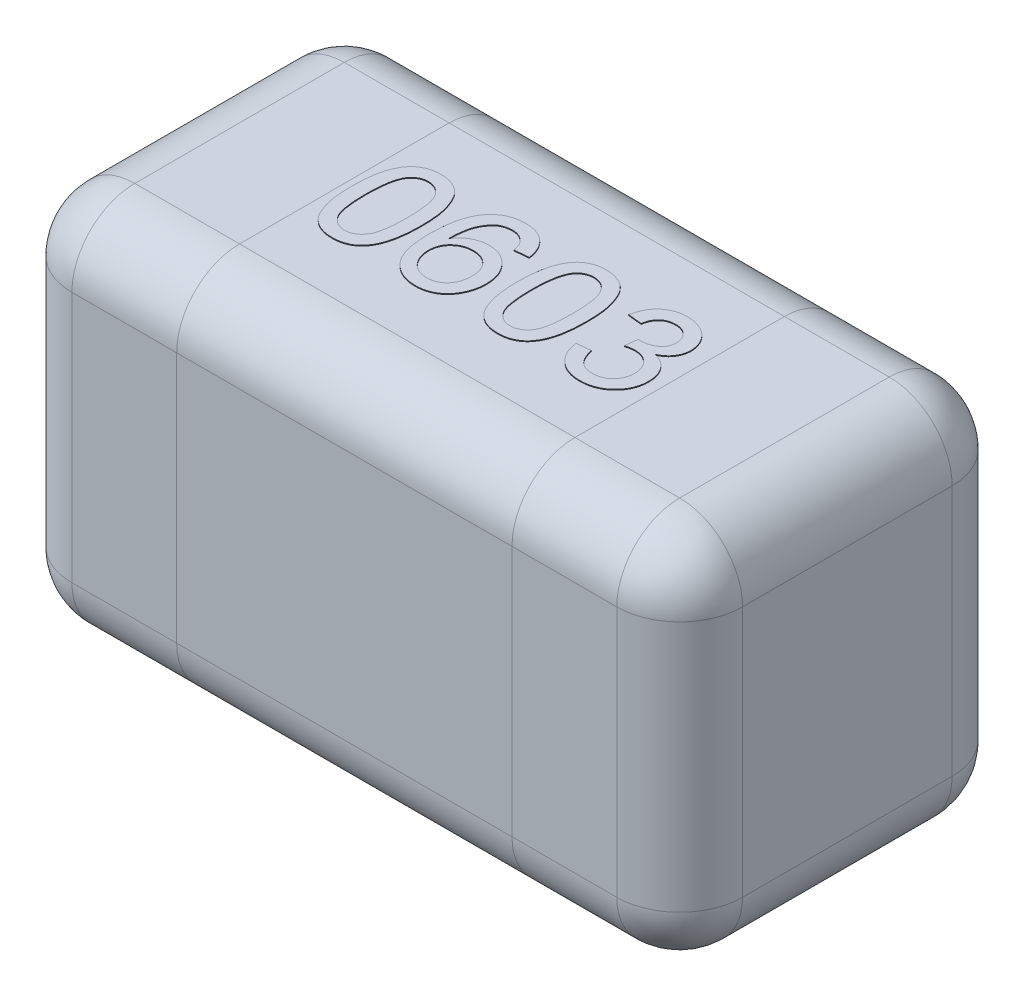
SolidWorks part; units mm, degrees
ref_plane "Front" through (0, 0, 0) normal (0, 0, 1) x (1, 0, 0)
ref_plane "Top" through (0, 0, 0) normal (0, 1, 0) x (1, 0, 0)
ref_plane "Right" through (0, 0, 0) normal (1, 0, 0) x (0, 0, -1)
sketch "Sketch1" plane through (0, 0, 0) normal (0, 1, 0) x (1, 0, 0)
  line L0 (0, -5.3126) -> (0, 5.729) construction
  line L1 (-6.1479, 0) -> (7.7291, 0) construction
  line L3 (-0.8, 0.4) -> (0.8, 0.4)
  line L4 (-0.8, 0.4) -> (-0.8, -0.4)
  line L5 (-0.8, -0.4) -> (0.8, -0.4)
  line L6 (0.8, 0.4) -> (0.8, -0.4)
  dimension "D1" = 1.6
  dimension "D2" = 0.8
extrude "Extrude1" add sketch "Sketch1" along normal blind 0.9
fillet "Fillet1" radius 0.15 12 edges at (0, 0.9, 0.4) (-0.8, 0.45, -0.4) (0, 0, -0.4) (-0.8, 0, 0) (-0.8, 0.45, 0.4) (0, 0, 0.4) (0.8, 0.45, 0.4) (0.8, 0.45, -0.4) (0.8, 0, 0) (0, 0.9, -0.4) (0.8, 0.9, 0) (-0.8, 0.9, 0)
sketch "Sketch2" plane through (0, 0, 0.4) normal (0, 0, 1) x (1, 0, 0)
  line L0 (-0.65, 0.9) -> (0.65, 0.9) construction
  line L1 (-0.4, 0.9) -> (0.4, 0.9)
  line L2 (-0.4, 0.9) -> (-0.4, 0)
  line L3 (-0.4, 0) -> (0.4, 0)
  line L4 (0.4, 0.9) -> (0.4, 0)
  line L5 (0.65, 0) -> (-0.65, 0) construction
  line L6 (-0.8, 0.15) -> (-0.8, 0.75) construction
  line L7 (0, -0.2963) -> (0, 3.0124) construction
  dimension "D1" = 0.4
split line "Split Line1"
sketch "Sketch3" plane through (0, 0.9, 0) normal (0, 1, 0) x (1, 0, 0)
  text T0 "0603" font "Arial" height in points 1
  dimension "D1" = 0.4
  dimension "D2" = 0.125
extrude "Extrude2" add sketch "Sketch3" along normal blind 0.002
